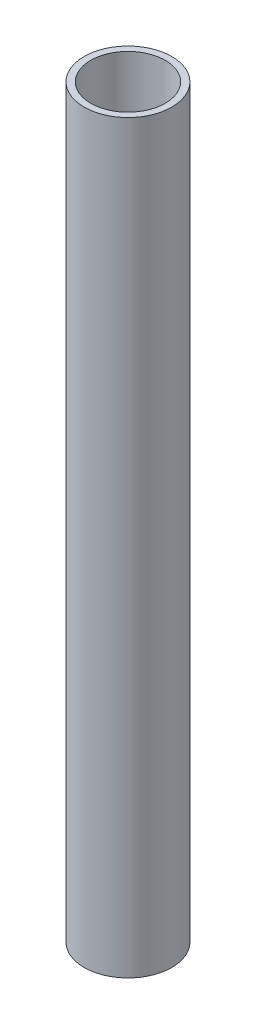
SolidWorks part; units mm, degrees
ref_plane "Front Plane" through (0, 0, 0) normal (0, 0, 1) x (1, 0, 0)
ref_plane "Top Plane" through (0, 0, 0) normal (0, 1, 0) x (1, 0, 0)
ref_plane "Right Plane" through (0, 0, 0) normal (1, 0, 0) x (0, 0, -1)
sketch "Sketch1" plane through (0, 0, 0) normal (0, 1, 0) x (1, 0, 0)
  circle A0 centre (0, 0) radius 12.7
  circle A2 centre (0, 0) radius 10.795
  dimension "D1" = 25.4
  dimension "D2" = 21.59
extrude "Boss-Extrude1" add sketch "Sketch1" along normal blind 215.9
